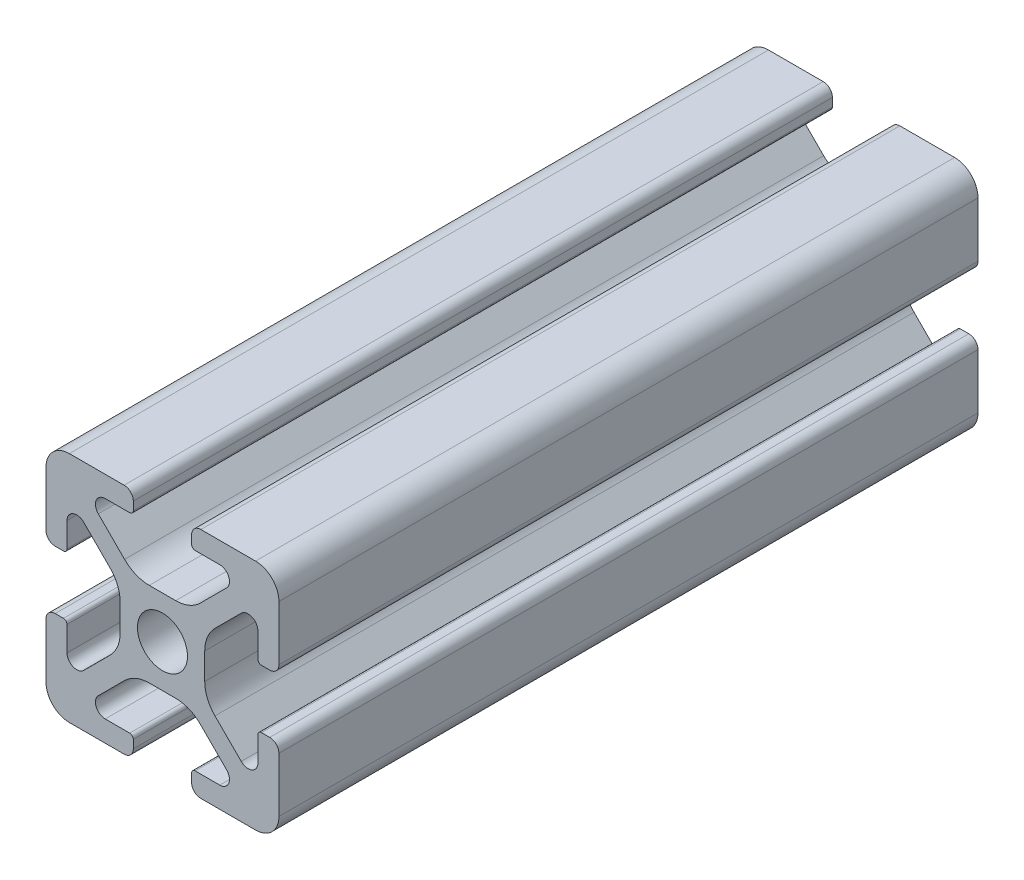
SolidWorks part; units mm, degrees
ref_plane "Front Plane" through (0, 0, 0) normal (0, 0, 1) x (1, 0, 0)
ref_plane "Top Plane" through (0, 0, 0) normal (0, 1, 0) x (1, 0, 0)
ref_plane "Right Plane" through (0, 0, 0) normal (1, 0, 0) x (0, 0, -1)
sketch "Sketch1" plane through (0, 0, 0) normal (0, 0, 1) x (1, 0, 0)
  line L2 (-9.9949, 7.9883) -> (-9.9949, 3.2893)
  line L3 (-7.9883, 9.9949) -> (-3.2893, 9.9949)
  line L4 (-2.5019, 9.2075) -> (-2.5019, 8.4963)
  line L5 (-2.8067, 8.1915) -> (-4.9149, 8.1915)
  line L6 (-5.5076, 6.7606) -> (-3.2528, 4.5058)
  line L7 (-6.7606, 5.5076) -> (-4.5058, 3.2528)
  line L8 (-8.1915, 4.9149) -> (-8.1915, 2.8067)
  line L9 (-8.4963, 2.5019) -> (-9.2075, 2.5019)
  line L11 (-1.1334, 3.6279) -> (1.1334, 3.6279)
  line L12 (-3.6279, 1.1334) -> (-3.6279, -1.1334)
  line L13 (8.4963, 2.5019) -> (9.2075, 2.5019)
  line L14 (8.1915, 4.9149) -> (8.1915, 2.8067)
  line L15 (9.9949, 7.9883) -> (9.9949, 3.2893)
  line L16 (7.9883, 9.9949) -> (3.2893, 9.9949)
  line L17 (2.5019, 9.2075) -> (2.5019, 8.4963)
  line L18 (2.8067, 8.1915) -> (4.9149, 8.1915)
  line L19 (3.6279, 1.1334) -> (3.6279, -1.1334)
  line L20 (5.5076, 6.7606) -> (3.2528, 4.5058)
  line L21 (6.7606, 5.5076) -> (4.5058, 3.2528)
  line L22 (-8.4963, -2.5019) -> (-9.2075, -2.5019)
  line L23 (-8.1915, -4.9149) -> (-8.1915, -2.8067)
  line L24 (-6.7606, -5.5076) -> (-4.5058, -3.2528)
  line L25 (-5.5076, -6.7606) -> (-3.2528, -4.5058)
  line L26 (-2.8067, -8.1915) -> (-4.9149, -8.1915)
  line L27 (-2.5019, -9.2075) -> (-2.5019, -8.4963)
  line L28 (-7.9883, -9.9949) -> (-3.2893, -9.9949)
  line L29 (-9.9949, -7.9883) -> (-9.9949, -3.2893)
  line L30 (9.9949, -7.9883) -> (9.9949, -3.2893)
  line L31 (7.9883, -9.9949) -> (3.2893, -9.9949)
  line L32 (2.5019, -9.2075) -> (2.5019, -8.4963)
  line L33 (2.8067, -8.1915) -> (4.9149, -8.1915)
  line L34 (5.5076, -6.7606) -> (3.2528, -4.5058)
  line L35 (6.7606, -5.5076) -> (4.5058, -3.2528)
  line L36 (8.1915, -4.9149) -> (8.1915, -2.8067)
  line L37 (8.4963, -2.5019) -> (9.2075, -2.5019)
  line L38 (-1.1334, -3.6279) -> (1.1334, -3.6279)
  circle A0 centre (0, 0) radius 2.1463
  arc A1 (-9.9949, 7.9883) -> (-7.9883, 9.9949) centre (-7.9883, 7.9883) cw
  arc A2 (-6.7606, 5.5076) -> (-8.1915, 4.9149) centre (-7.3533, 4.9149) ccw
  arc A3 (-4.9149, 8.1915) -> (-5.5076, 6.7606) centre (-4.9149, 7.3533) ccw
  arc A4 (-3.2893, 9.9949) -> (-2.5019, 9.2075) centre (-3.2893, 9.2075) cw
  arc A5 (-9.9949, 3.2893) -> (-9.2075, 2.5019) centre (-9.2075, 3.2893) ccw
  arc A6 (-8.1915, 2.8067) -> (-8.4963, 2.5019) centre (-8.4963, 2.8067) cw
  arc A7 (-2.5019, 8.4963) -> (-2.8067, 8.1915) centre (-2.8067, 8.4963) cw
  arc A8 (-1.1334, 3.6279) -> (-3.2528, 4.5058) centre (-1.1334, 6.6251) cw
  arc A9 (-3.6279, 1.1334) -> (-4.5058, 3.2528) centre (-6.6251, 1.1334) ccw
  arc A10 (8.1915, 2.8067) -> (8.4963, 2.5019) centre (8.4963, 2.8067) ccw
  arc A11 (9.9949, 3.2893) -> (9.2075, 2.5019) centre (9.2075, 3.2893) cw
  arc A12 (9.9949, 7.9883) -> (7.9883, 9.9949) centre (7.9883, 7.9883) ccw
  arc A13 (3.2893, 9.9949) -> (2.5019, 9.2075) centre (3.2893, 9.2075) ccw
  arc A14 (2.5019, 8.4963) -> (2.8067, 8.1915) centre (2.8067, 8.4963) ccw
  arc A15 (1.1334, 3.6279) -> (3.2528, 4.5058) centre (1.1334, 6.6251) ccw
  arc A16 (3.6279, 1.1334) -> (4.5058, 3.2528) centre (6.6251, 1.1334) cw
  arc A17 (6.7606, 5.5076) -> (8.1915, 4.9149) centre (7.3533, 4.9149) cw
  arc A18 (4.9149, 8.1915) -> (5.5076, 6.7606) centre (4.9149, 7.3533) cw
  arc A19 (-3.6279, -1.1334) -> (-4.5058, -3.2528) centre (-6.6251, -1.1334) cw
  arc A20 (-1.1334, -3.6279) -> (-3.2528, -4.5058) centre (-1.1334, -6.6251) ccw
  arc A21 (-2.5019, -8.4963) -> (-2.8067, -8.1915) centre (-2.8067, -8.4963) ccw
  arc A22 (-8.1915, -2.8067) -> (-8.4963, -2.5019) centre (-8.4963, -2.8067) ccw
  arc A23 (-9.9949, -3.2893) -> (-9.2075, -2.5019) centre (-9.2075, -3.2893) cw
  arc A24 (-3.2893, -9.9949) -> (-2.5019, -9.2075) centre (-3.2893, -9.2075) ccw
  arc A25 (-4.9149, -8.1915) -> (-5.5076, -6.7606) centre (-4.9149, -7.3533) cw
  arc A26 (-6.7606, -5.5076) -> (-8.1915, -4.9149) centre (-7.3533, -4.9149) cw
  arc A27 (-9.9949, -7.9883) -> (-7.9883, -9.9949) centre (-7.9883, -7.9883) ccw
  arc A28 (9.9949, -7.9883) -> (7.9883, -9.9949) centre (7.9883, -7.9883) cw
  arc A29 (6.7606, -5.5076) -> (8.1915, -4.9149) centre (7.3533, -4.9149) ccw
  arc A30 (4.9149, -8.1915) -> (5.5076, -6.7606) centre (4.9149, -7.3533) ccw
  arc A31 (3.2893, -9.9949) -> (2.5019, -9.2075) centre (3.2893, -9.2075) cw
  arc A32 (9.9949, -3.2893) -> (9.2075, -2.5019) centre (9.2075, -3.2893) ccw
  arc A33 (8.1915, -2.8067) -> (8.4963, -2.5019) centre (8.4963, -2.8067) cw
  arc A34 (2.5019, -8.4963) -> (2.8067, -8.1915) centre (2.8067, -8.4963) cw
  arc A35 (1.1334, -3.6279) -> (3.2528, -4.5058) centre (1.1334, -6.6251) cw
  arc A36 (3.6279, -1.1334) -> (4.5058, -3.2528) centre (6.6251, -1.1334) ccw
extrude "Boss-Extrude1" add sketch "Sketch1" along normal mid plane 60
